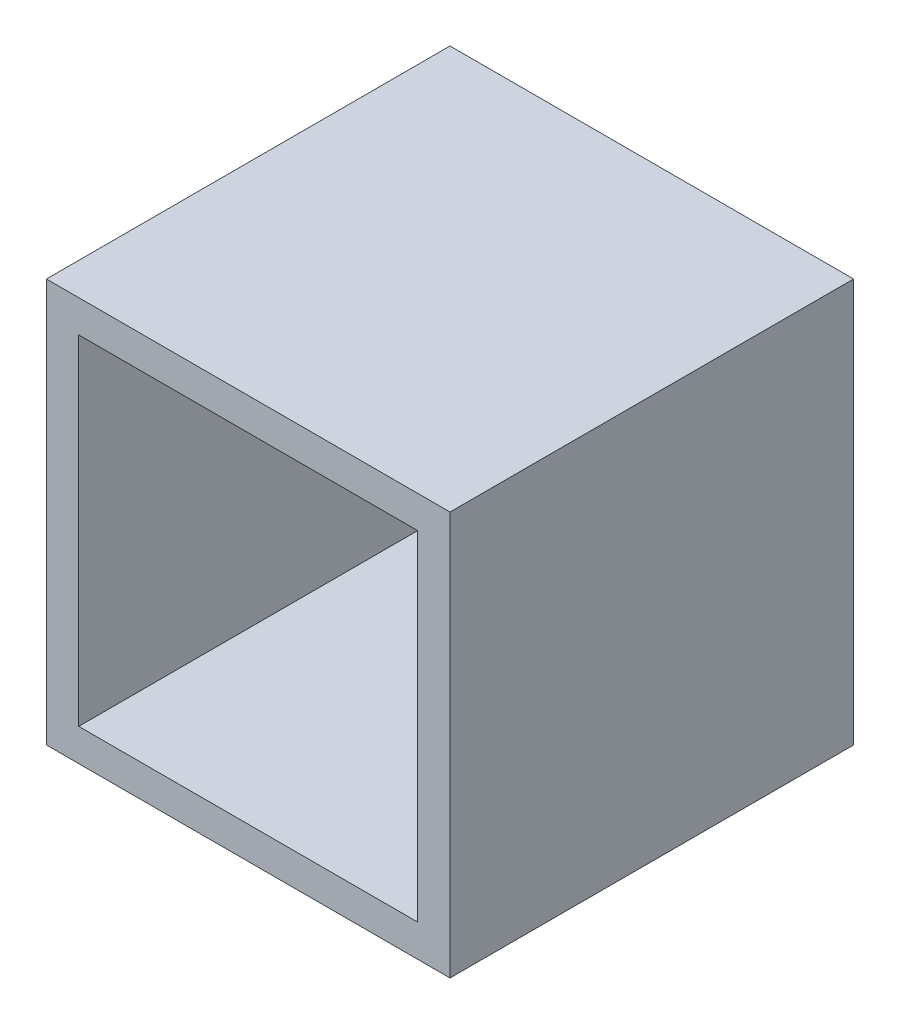
SolidWorks part; units mm, degrees
ref_plane "Front" through (0, 0, 0) normal (0, 0, 1) x (1, 0, 0)
ref_plane "Top" through (0, 0, 0) normal (0, 1, 0) x (1, 0, 0)
ref_plane "Right" through (0, 0, 0) normal (1, 0, 0) x (0, 0, -1)
sketch "Sketch1" plane through (0, 0, 0) normal (0, 0, 1) x (1, 0, 0)
  line L0 (0, 0) -> (0, 36.4553) construction
  line L1 (-5, 5) -> (5, 5)
  line L2 (-5, 5) -> (-5, -5)
  line L3 (-5, -5) -> (5, -5)
  line L4 (5, 5) -> (5, -5)
  line L5 (0, 0) -> (43.2883, 0) construction
  point P5 (0, 5)
  point P10 (5, 0)
  dimension "D1" = 10
  dimension "D2" = 10
extrude "Boss-Extrude1" add sketch "Sketch1" along normal blind 0.8
sketch "Sketch2" plane through (0, 0, 0.8) normal (0, 0, 1) x (1, 0, 0)
  line L1 (-5, 5) -> (5, 5)
  line L2 (-5, 5) -> (-5, -5)
  line L3 (-5, -5) -> (5, -5)
  line L4 (5, 5) -> (5, -5)
  line L5 (-4.2, 4.2) -> (4.2, 4.2)
  line L6 (-4.2, 4.2) -> (-4.2, -4.2)
  line L7 (-4.2, -4.2) -> (4.2, -4.2)
  line L8 (4.2, 4.2) -> (4.2, -4.2)
  dimension "D1" = 0.8
  dimension "D2" = 0.8
  dimension "D3" = 0.8
  dimension "D4" = 0.8
extrude "Boss-Extrude2" add sketch "Sketch2" along normal blind 9.2
